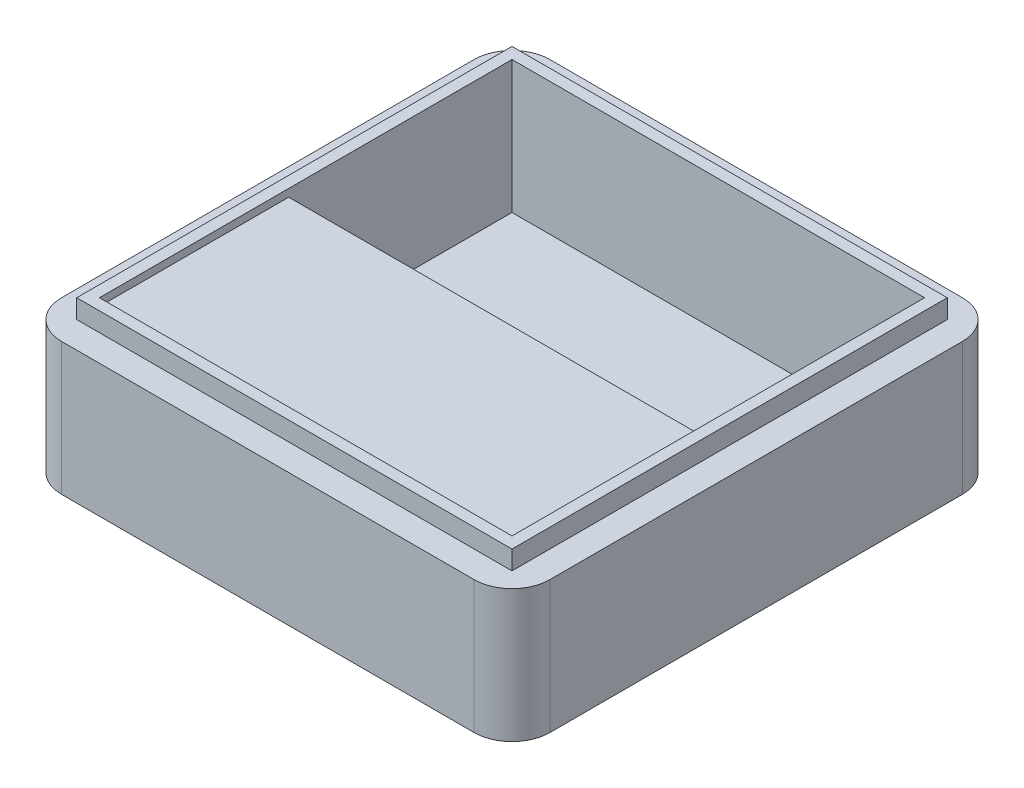
SolidWorks part; units mm, degrees
ref_plane "Front Plane" through (0, 0, 0) normal (0, 0, 1) x (1, 0, 0)
ref_plane "Top Plane" through (0, 0, 0) normal (0, 1, 0) x (1, 0, 0)
ref_plane "Right Plane" through (0, 0, 0) normal (1, 0, 0) x (0, 0, -1)
sketch "Sketch1" plane through (0, 0, 0) normal (0, 1, 0) x (1, 0, 0)
  line L1 (-57.5, -57.5) -> (57.5, -57.5)
  line L2 (-57.5, -57.5) -> (-57.5, 57.5)
  line L3 (-57.5, 57.5) -> (57.5, 57.5)
  line L4 (57.5, -57.5) -> (57.5, 57.5)
  line L5 (-57.5, -57.5) -> (57.5, 57.5) construction
  line L6 (-57.5, 57.5) -> (57.5, -57.5) construction
  point P0 (0, 0)
  dimension "D1" = 115
extrude "Boss-Extrude2" add sketch "Sketch1" along normal blind 5
sketch "Sketch3" plane through (0, 0, 0) normal (0, -1, 0) x (1, 0, 0)
  line L1 (-64.5, -64.5) -> (64.5, -64.5)
  line L2 (-64.5, -64.5) -> (-64.5, 64.5)
  line L3 (-64.5, 64.5) -> (64.5, 64.5)
  line L4 (64.5, -64.5) -> (64.5, 64.5)
  line L5 (-64.5, -64.5) -> (64.5, 64.5) construction
  line L6 (-64.5, 64.5) -> (64.5, -64.5) construction
  point P0 (0, 0)
  dimension "D1" = 129
extrude "Boss-Extrude3" add sketch "Sketch3" along normal blind 35
sketch "Sketch4" plane through (0, 5, 0) normal (0, 1, 0) x (1, 0, 0)
  line L8 (54.5, -54.5) -> (54.5, 54.5)
  line L9 (54.5, 54.5) -> (-54.5, 54.5)
  line L10 (-54.5, 54.5) -> (-54.5, -54.5)
  line L11 (-54.5, -54.5) -> (54.5, -54.5)
  line L12 (54.5, -54.5) -> (54.5, 54.5)
  line L13 (54.5, 54.5) -> (-54.5, 54.5)
  line L14 (-54.5, 54.5) -> (-54.5, -54.5)
  line L15 (-54.5, -54.5) -> (54.5, -54.5)
  dimension "D1" = 3
extrude "Cut-Extrude1" cut sketch "Sketch4" against normal offset from surface (35 mm away) 5 up to face at (0, -35, 0)
fillet "Fillet1" radius 10 4 edges at (-64.5, -17.5, 64.5) (-64.5, -17.5, -64.5) (64.5, -17.5, -64.5) (64.5, -17.5, 64.5)
sketch "Sketch6" plane through (0, 0, 54.5) normal (0, 0, -1) x (-1, 0, 0)
  line L1 (-54.5, -30) -> (-54.5, 3)
  line L4 (-54.5, -30) -> (54.5, -30)
  line L5 (54.5, -30) -> (54.5, 5)
  line L6 (54.5, 5) -> (-54.5, 5)
  line L7 (-54.5, 5) -> (-54.5, -30)
  line L8 (-54.5, -30) -> (54.5, -30)
  line L15 (-54.5, 3) -> (54.5, 3)
  line L16 (54.5, -35) -> (54.5, 0) construction
  line L17 (54.5, 3) -> (54.5, -30)
  line L18 (54.5, 5) -> (-54.5, 5) construction
  dimension "D2" = 2
  dimension "D1" = 0
extrude "Boss-Extrude5" add sketch "Sketch6" along normal blind 50
